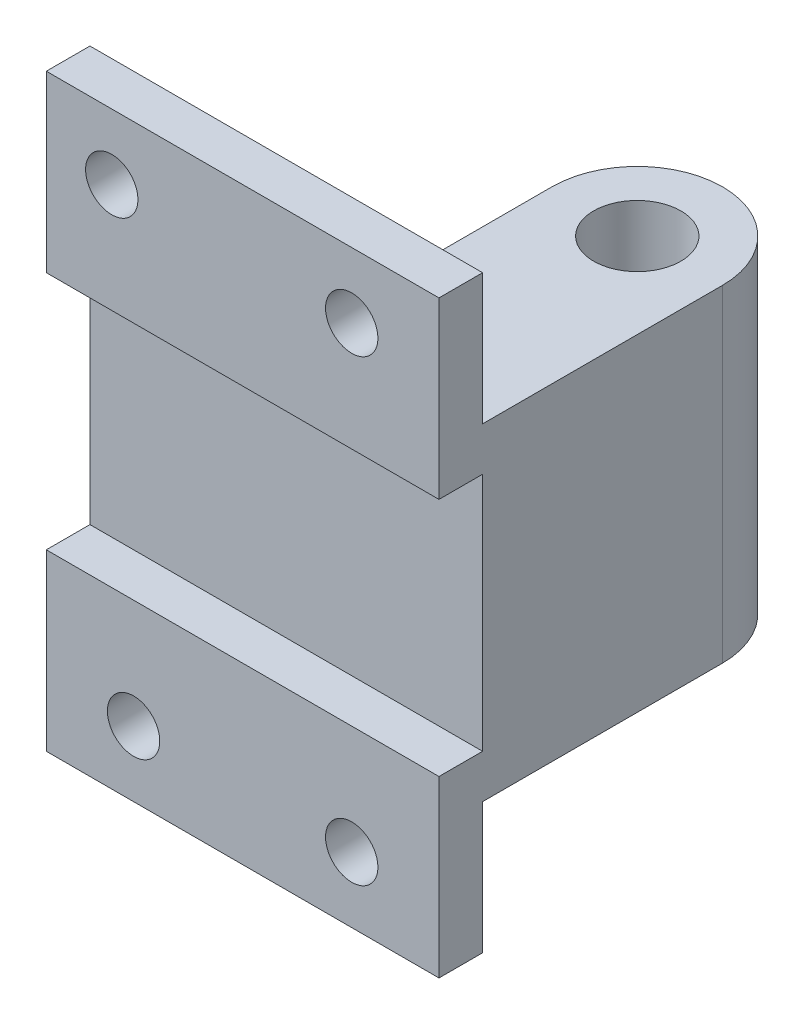
SolidWorks part; units mm, degrees
ref_plane "Front Plane" through (0, 0, 0) normal (0, 0, 1) x (1, 0, 0)
ref_plane "Top Plane" through (0, 0, 0) normal (0, 1, 0) x (1, 0, 0)
ref_plane "Right Plane" through (0, 0, 0) normal (1, 0, 0) x (0, 0, -1)
sketch "Sketch4" plane through (0, 0, 0) normal (0, 1, 0) x (1, 0, 0)
  line L1 (0, 0) -> (90, 0)
  line L2 (0, 0) -> (0, 10)
  line L3 (0, 10) -> (90, 10)
  line L4 (90, 0) -> (90, 10)
  dimension "D1" = 90
  dimension "D2" = 10
extrude "Boss-Extrude3" add sketch "Sketch4" along normal blind 135
sketch "Sketch5" plane through (0, 0, 0) normal (1, 0, 0) x (0, 0, -1)
  line L0 (23.1653, 67.5) -> (-11.7414, 67.5) construction
  line L1 (0, 0) -> (0, 40)
  line L2 (0, 135) -> (0, 0) construction
  line L3 (0, 40) -> (10, 40)
  line L4 (10, 135) -> (10, 0) construction
  line L5 (10, 40) -> (10, 95)
  line L6 (10, 95) -> (0, 95)
  line L7 (0, 95) -> (0, 135)
  line L8 (0, 135) -> (10, 135)
  line L9 (10, 135) -> (10, 105)
  line L10 (10, 105) -> (20, 105)
  line L11 (20, 105) -> (20, 30)
  line L12 (20, 30) -> (10, 30)
  line L13 (10, 30) -> (10, 0)
  line L14 (10, 0) -> (0, 0)
  dimension "D1" = 40
  dimension "D2" = 55
  dimension "D3" = 30
  dimension "D4" = 10
  dimension "D5" = 75
extrude "Boss-Extrude4" add sketch "Sketch5" along normal blind 90
sketch "Sketch6" plane through (0, 0, 0) normal (-1, 0, 0) x (0, 0, 1)
  line L5 (-10, 30) -> (0, 30)
  line L6 (0, 135) -> (0, 0) construction
  line L7 (0, 30) -> (0, 40)
  line L8 (0, 40) -> (-10, 40)
  line L9 (-10, 40) -> (-10, 95)
  line L10 (-10, 95) -> (0, 95)
  line L11 (0, 95) -> (0, 40)
  dimension "D1" = 10
  dimension "D2" = 55
extrude "Cut-Extrude3" cut sketch "Sketch6" against normal blind 130 contours L10 L9 L8
sketch "Sketch7" plane through (0, 30, 0) normal (0, -1, 0) x (1, 0, 0)
  line L0 (90, -20) -> (90, -65)
  line L1 (50.8917, -65) -> (50.8917, -20)
  line L2 (90, -20) -> (0, -20) construction
  line L3 (50.8917, -20) -> (90, -20)
  arc A0 (90, -65) -> (50.8917, -65) centre (70.4458, -65) cw
  dimension "D2" = 19.5542
  dimension "D1" = 45
extrude "Boss-Extrude5" add sketch "Sketch7" against normal blind 75 contours L3 L0 A0 L1
sketch "Sketch8" plane through (0, 30, 0) normal (0, -1, 0) x (1, 0, 0)
  line L0 (70.4458, -84.5542) -> (70.4458, -10) construction
  line L1 (90, -10) -> (0, -10) construction
  arc A0 (50.8917, -65) -> (90, -65) centre (70.4458, -65) ccw construction
  circle A1 centre (70.4458, -65) radius 10
  dimension "D1" = 20
extrude "Cut-Extrude4" cut sketch "Sketch8" against normal blind 95
ref_plane "Plane1" through (50.8917, 105, -65) normal (0, -1, 0) x (-1, 0, 0)
sketch "Sketch11" plane through (0, 0, -10) normal (0, 0, -1) x (-1, 0, 0)
  line L0 (-20, 15) -> (-70, 15) construction
  line L1 (-90, 71.9386) -> (0, 71.9386)
  line L4 (-90, 105) -> (-90, 30) construction
  line L5 (0, 30) -> (0, 105) construction
  line L6 (0, 30) -> (0, 0) construction
  line L7 (0, 15) -> (-20, 15) construction
  circle A2 centre (-20, 15) radius 6
  circle A3 centre (-70, 15) radius 6
  dimension "D3" = 12
  dimension "D4" = 12
  dimension "D1" = 50
  dimension "D2" = 20
extrude "Cut-Extrude5" cut sketch "Sketch11" against normal blind 95 contours A3 | A2
sketch "Sketch12" plane through (0, 0, -10) normal (0, 0, -1) x (-1, 0, 0)
  line L0 (-90, 135) -> (-90, 120) construction
  line L1 (-90, 135) -> (-90, 105) construction
  line L2 (-90, 120) -> (-70, 120) construction
  line L3 (-70, 120) -> (-15, 120) construction
  circle A0 centre (-70, 120) radius 6
  circle A1 centre (-15, 120) radius 6
  dimension "D2" = 12
  dimension "D4" = 12
  dimension "D1" = 20
  dimension "D3" = 55
extrude "Cut-Extrude6" cut sketch "Sketch12" against normal blind 95
sketch "Sketch13" plane through (0, 30, 0) normal (0, -1, 0) x (1, 0, 0)
  line L0 (0, -10) -> (45, -10) construction
  line L1 (90, -10) -> (0, -10) construction
  line L2 (45, -10) -> (45, -20)
  line L3 (50.8917, -20) -> (0, -20) construction
  line L4 (45, -20) -> (39, -20)
  line L5 (39, -20) -> (39, -10)
  line L6 (39, -10) -> (45, -10)
  dimension "D1" = 6
extrude "Boss-Extrude6" add sketch "Sketch13" along normal blind 30
sketch "Sketch14" plane through (39, 0, 0) normal (-1, 0, 0) x (0, 0, 1)
  line L0 (-20, 30) -> (-9.0337, -2.8191)
  line L1 (-9.0337, -2.8191) -> (-23.0679, -4.0279)
  line L2 (-23.0679, -4.0279) -> (-23.0679, 30)
  line L5 (-23.0679, 30) -> (-20, 30)
extrude "Cut-Extrude7" cut sketch "Sketch14" against normal blind 30
ref_plane "Plane2" through (0, 70, 0) normal (0, 1, 0) x (1, 0, 0)
sketch "Sketch16" plane through (0, 70, 0) normal (0, 1, 0) x (1, 0, 0)
  line L0 (50.0907, 21.4719) -> (50.0907, 65.8944)
  line L1 (56.5789, 78.5944) -> (-4.0854, 78.5944)
  line L2 (-4.0854, 78.5944) -> (-4.0854, 21.4719)
  line L3 (-4.0854, 21.4719) -> (50.0907, 21.4719)
  arc A0 (50.0907, 65.8944) -> (56.5789, 78.5944) centre (65.7644, 65.8944) cw
extrude "Boss-Extrude7" add sketch "Sketch16" along normal mid plane 6
sketch "Sketch17" plane through (0, 67, 0) normal (0, -1, 0) x (1, 0, 0)
  line L0 (55.9203, -78.091) -> (-4.0854, -21.4719)
  line L1 (-4.0854, -21.4719) -> (-4.0854, -120.6105)
  line L4 (55.9203, -78.091) -> (55.9203, -116.4062)
  line L5 (55.9203, -116.4062) -> (-4.0854, -120.6105)
extrude "Cut-Extrude10" cut sketch "Sketch17" against normal mid plane 36
sketch "Sketch18" plane through (0, 105, 0) normal (0, 1, 0) x (1, 0, 0)
  line L0 (50.8917, 20) -> (0, 20) construction
  line L1 (39, 20) -> (45, 20)
  line L2 (39, 20) -> (39, 10)
  line L3 (39, 10) -> (45, 10)
  line L4 (45, 20) -> (45, 10)
  line L5 (90, 10) -> (0, 10) construction
  dimension "D1" = 6
extrude "Boss-Extrude8" add sketch "Sketch18" along normal blind 30
sketch "Sketch19" plane through (39, 0, 0) normal (-1, 0, 0) x (0, 0, 1)
  line L0 (-20, 105) -> (-10, 135)
  line L1 (-10, 135) -> (-32.2289, 136.3528)
  line L2 (-32.2289, 136.3528) -> (-34.0263, 106.8187)
  line L3 (-34.0263, 106.8187) -> (-20, 105)
extrude "Cut-Extrude11" cut sketch "Sketch19" against normal blind 30
sketch "Sketch20" plane through (0, 67, 0) normal (0, -1, 0) x (1, 0, 0)
  line L1 (0, -20) -> (50.0907, -20)
  line L2 (0, -20) -> (0, -21.4719)
  line L3 (0, -21.4719) -> (50.0907, -21.4719)
  line L4 (50.0907, -20) -> (50.0907, -21.4719)
extrude "Boss-Extrude9" add sketch "Sketch20" against normal blind 6
sketch "Sketch21" plane through (0, 67, 0) normal (0, -1, 0) x (1, 0, 0)
  line L0 (0, -20) -> (0, -25.3267)
  line L1 (54.1595, -76.4296) -> (-4.0854, -21.4719) construction
  line L2 (0, -25.3267) -> (-9.7932, -25.3267)
  line L3 (-9.7932, -25.3267) -> (-9.7932, -20)
  line L4 (-9.7932, -20) -> (0, -20)
extrude "Cut-Extrude12" cut sketch "Sketch21" against normal blind 6
